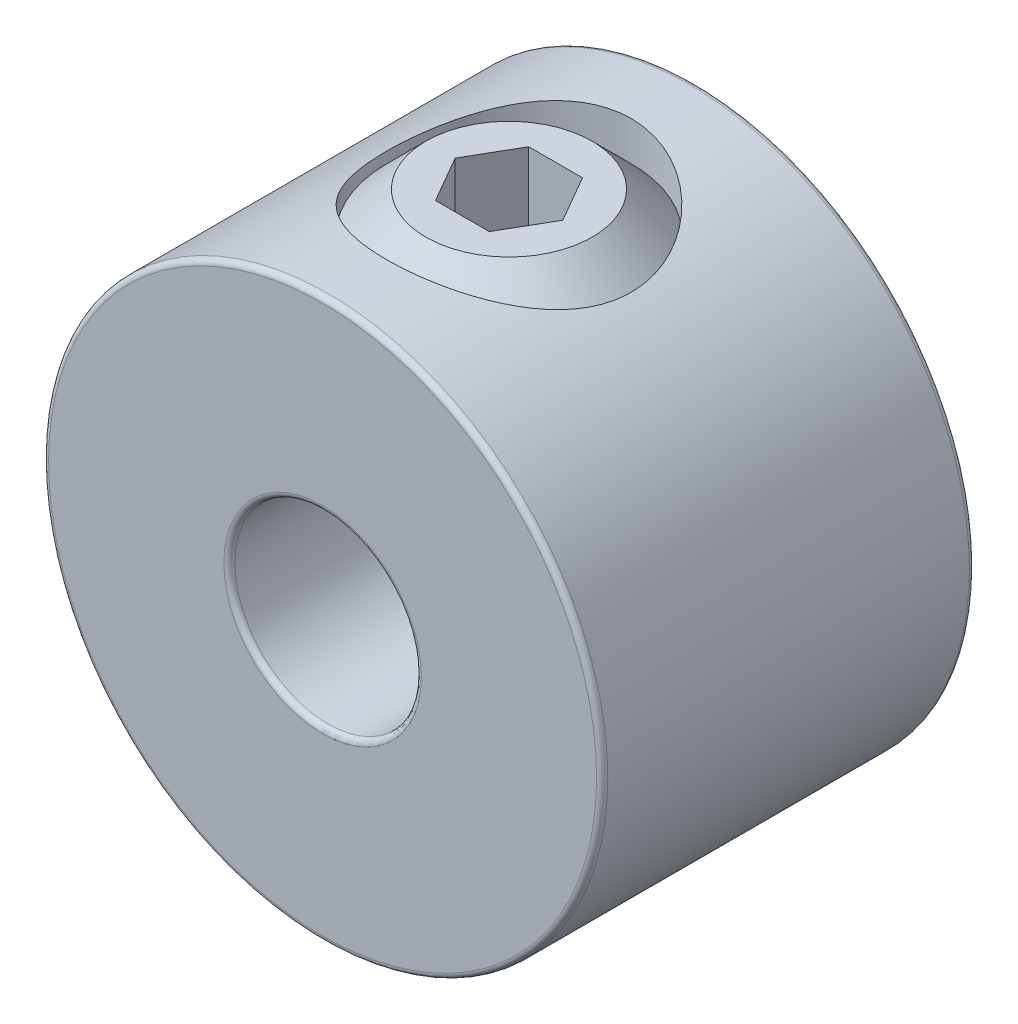
SolidWorks part; units mm, degrees
ref_plane "Front Plane" through (0, 0, 0) normal (0, 0, 1) x (1, 0, 0)
ref_plane "Top Plane" through (0, 0, 0) normal (0, 1, 0) x (1, 0, 0)
ref_plane "Right Plane" through (0, 0, 0) normal (1, 0, 0) x (0, 0, -1)
sketch "Sketch1" plane through (0, 0, 0) normal (0, 0, 1) x (1, 0, 0)
  circle A0 centre (0, 0) radius 4.7625
  circle A1 centre (0, 0) radius 1.5875
  point P4 (4.7625, 0)
  dimension "Bore Dia" = 3.175
  dimension "OD" = 9.525
extrude "Extrude1" add sketch "Sketch1" along normal mid plane 6.35
sketch "Sketch2" plane through (41.275, 0, 0) normal (0, -1, 0) x (0, 0, -1)
  line L0 (3.175, -41.275) -> (-3.175, -41.275) construction
  line L1 (-3.175, -36.5125) -> (-3.175, -46.0375) construction
  line L2 (3.175, -46.0375) -> (3.175, -36.5125) construction
  circle A0 centre (0, -41.275) radius 2.0828
  point P7 (0, -43.3578)
  dimension "Set Screw Dia" = 4.1656
extrude "Cut-Extrude1" cut sketch "Sketch2" against normal through all
fillet "Fillet1" radius 0.0953 4 edges at (1.5875, 0, -3.175) (1.5875, 0, 3.175) (4.7625, 0, -3.175) (4.7625, 0, 3.175)
sketch "Sketch3" plane through (0, 0, 0) normal (0, 0, 1) x (1, 0, 0)
  line L0 (-1.4164, 1.5875) -> (-0.7997, 1.5875)
  line L1 (0, 2.3872) -> (-0.7997, 1.5875)
  line L2 (0, 2.3872) -> (0, 4.7625)
  line L3 (0, 4.7625) -> (-1.4164, 4.7625)
  line L4 (-2.0828, 2.2539) -> (-2.0828, 4.0961)
  line L5 (0, 1.5875) -> (0, 0) construction
  line L6 (-2.0828, 2.2539) -> (-2.0828, 1.5875) construction
  line L7 (-2.0828, 1.5875) -> (-1.4164, 1.5875) construction
  line L8 (-2.0828, 4.0961) -> (-2.0828, 4.7625) construction
  line L9 (-1.4164, 1.5875) -> (-2.0828, 2.2539)
  line L10 (-2.0828, 4.0961) -> (-1.4164, 4.7625)
  line L11 (-2.0828, 4.7625) -> (-1.4164, 4.7625) construction
  line L12 (-0.7997, 1.5875) -> (0, 1.5875) construction
  line L13 (0, 1.5875) -> (0, 2.3872) construction
  circle A1 centre (0, 0) radius 1.5875 construction
  dimension "Screw Length" = 3.175
  dimension "D2" = 0.6664
  dimension "D1" = 0.7997
revolve "Revolve1" add sketch "Sketch3" angle 360 about L5
sketch "Sketch4" plane through (3.3734, 4.7625, 0) normal (0, -1, 0) x (0, 0, -1)
  line L1 (0, -2.4569) -> (-0.7938, -2.9152)
  line L2 (-0.7938, -2.9152) -> (-0.7938, -3.8317)
  line L3 (-0.7938, -3.8317) -> (0, -4.29)
  line L4 (0, -4.29) -> (0.7937, -3.8317)
  line L5 (0.7937, -3.8317) -> (0.7937, -2.9152)
  line L6 (0.7937, -2.9152) -> (0, -2.4569)
  circle A0 centre (0, -3.3734) radius 0.7937 construction
  circle A1 centre (0, -3.3734) radius 0.9165 construction
  dimension "D1" = 1.8331
  dimension "Hex Size" = 1.5875
extrude "Cut-Extrude2" cut sketch "Sketch4" along normal blind 1.5875
equation "\"D1@Fillet1\" = \"OD@Sketch1\"*.01"
equation "\"D1@Cut-Extrude2\" = \"Hex Size@Sketch4\""
equation "\"D2@Sketch3\" =(\"Set Screw Dia@Sketch2\"-\"D1@Sketch4\")/3.5"
equation "\"D1@Sketch3\" = \"D2@Sketch3\"*1.2"
